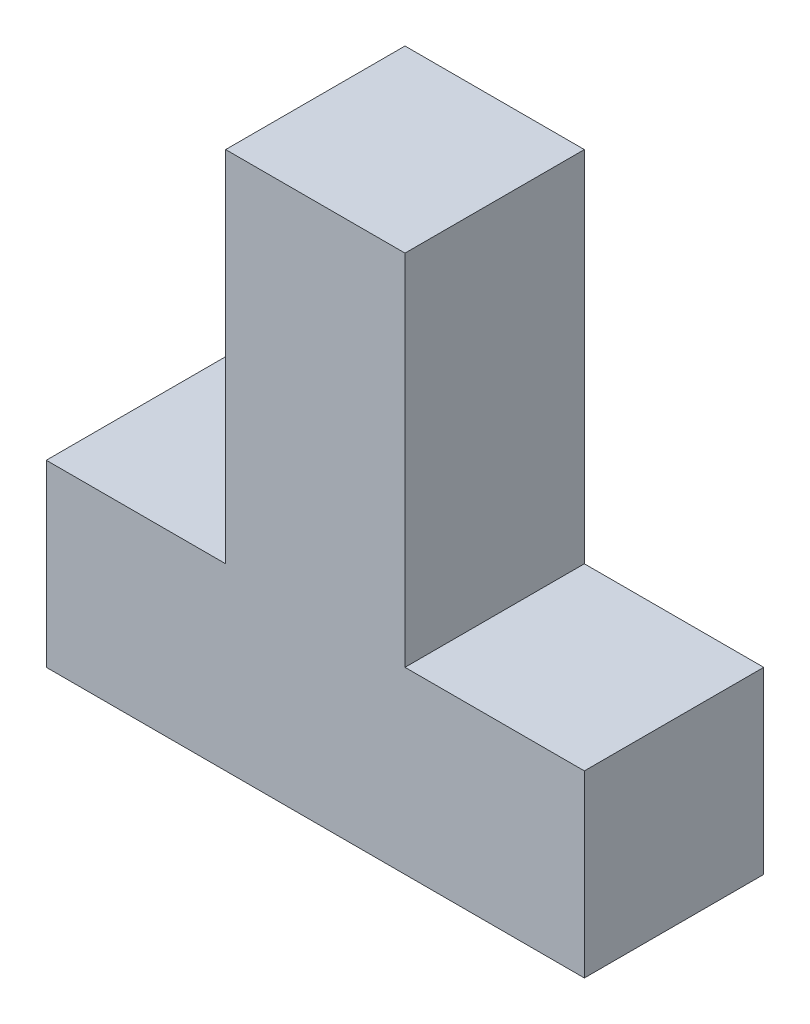
SolidWorks part; units mm, degrees
ref_plane "Front Plane" through (0, 0, 0) normal (0, 0, 1) x (1, 0, 0)
ref_plane "Top Plane" through (0, 0, 0) normal (0, 1, 0) x (1, 0, 0)
ref_plane "Right Plane" through (0, 0, 0) normal (1, 0, 0) x (0, 0, -1)
sketch "Sketch1" plane through (0, 0, 0) normal (0, 0, 1) x (1, 0, 0)
  line L50 (76.2, 0) -> (76.2, 25.4)
  line L51 (76.2, 25.4) -> (50.8, 25.4)
  line L52 (50.8, 25.4) -> (50.8, 76.2)
  line L53 (50.8, 76.2) -> (25.4, 76.2)
  line L54 (25.4, 76.2) -> (25.4, 25.4)
  line L55 (25.4, 25.4) -> (0, 25.4)
  line L56 (0, 25.4) -> (0, 0)
  line L57 (0, 0) -> (76.2, 0)
extrude "Boss-Extrude1" add sketch "Sketch1" along normal blind 25.4
